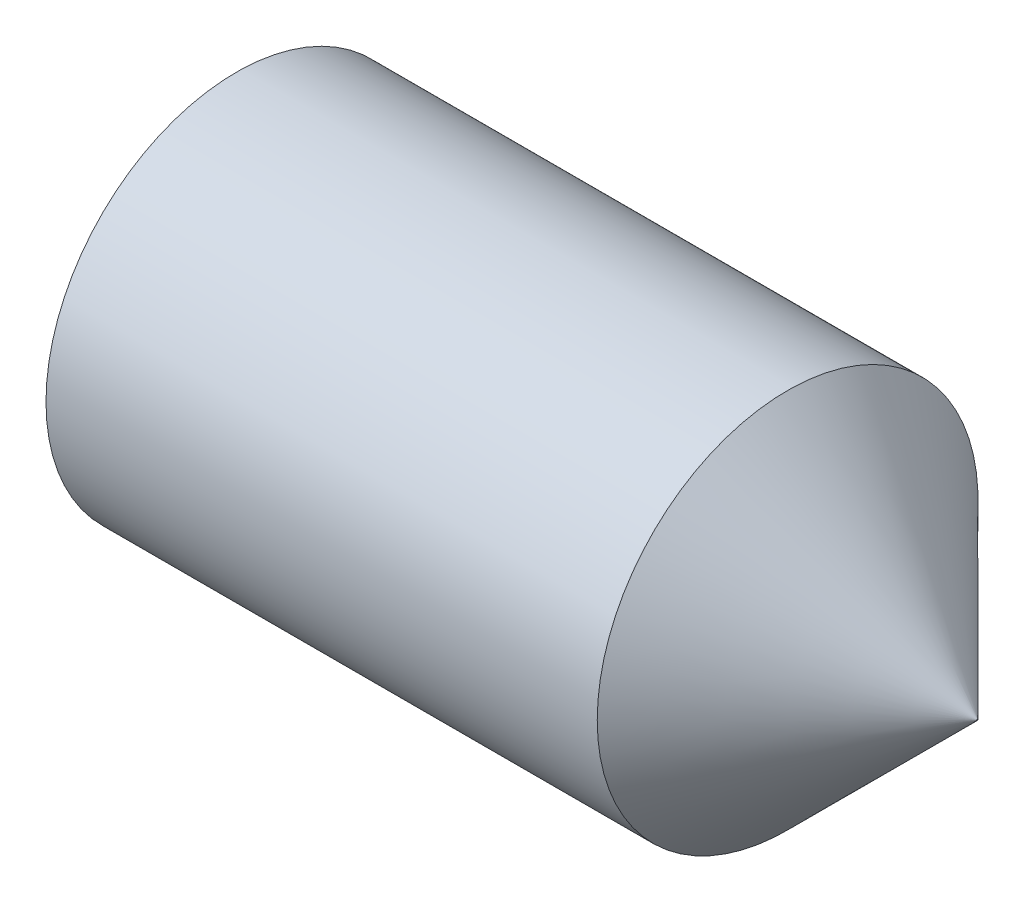
SolidWorks part; units mm, degrees
ref_plane "Plane1" through (0, 0, 0) normal (0, 0, 1) x (1, 0, 0)
ref_plane "Plane2" through (0, 0, 0) normal (0, 1, 0) x (1, 0, 0)
ref_plane "Plane3" through (0, 0, 0) normal (1, 0, 0) x (0, 0, -1)
sketch "BodySke" plane through (0, 0, 0) normal (0, 0, 1) x (1, 0, 0)
  line L0 (0, 0) -> (0, 1.2195)
  line L1 (0, 1.2195) -> (0.1619, 1.5)
  line L2 (0.1619, 1.5) -> (4.505, 1.5)
  line L3 (6, 0) -> (6, 0.005)
  line L4 (6, 0) -> (0, 0)
  line L5 (-12.7, 0) -> (88.9, 0) construction
  line L6 (6, 0.005) -> (4.505, 1.5)
  line L7 (0.5, 15.875) -> (0.5, -3.175) construction
  line L8 (0, -1.2195) -> (0.1619, -1.5) construction
  line L9 (6, -0.005) -> (4.505, -1.5) construction
  dimension "Cone_ang" = 90
  dimension "Length" = 6
  dimension "Diameter" = 3
  dimension "Drive_ch_ang" = 60
  dimension "Minor_dia" = 2.439
  dimension "Advance" = 0.5
  dimension "Tip_dia" = 0.01
revolve "BaseBody" add sketch "BodySke" angle 360 about L5
cosmetic thread "ThreadCosmetic" [suppressed] parameters "Thread_minor"=2.439
sketch "Sketch2" plane through (0, 0, 0) normal (-1, 0, 0) x (0, 0, 1)
  line L0 (0.433, 0.75) -> (-0.433, 0.75)
  line L1 (-0.433, 0.75) -> (-0.866, 0)
  line L2 (0.433, 0.75) -> (0.866, 0)
  line L3 (0.433, -0.75) -> (0.866, 0)
  line L4 (0.433, -0.75) -> (-0.433, -0.75)
  line L5 (-0.433, -0.75) -> (-0.866, 0)
  dimension "Hex_size" = 1.5
  dimension "D2" = 0.75
  dimension "D3" = 0.75
extrude "Hex" cut sketch "Sketch2" against normal blind 2.1
sketch "Sketch4" [suppressed] plane through (0, 4.7709, -0.5249) normal (-1, 0, 0) x (0, 0, 1)
  line L0 (0.5249, -4.7709) -> (10.6976, -4.7709)
  line L1 (0.5249, -4.7709) -> (6.6732, -1.2211) construction
  line L2 (0.5249, -4.7709) -> (5.6112, 4.0389)
  line L3 (8.9666, -2.6687) -> (10.2861, -1.9069)
  line L4 (6.5663, 1.4888) -> (7.8858, 2.2506)
  arc A0 (8.9666, -2.6687) -> (6.5663, 1.4888) centre (0.5249, -4.7709) ccw
  arc A1 (10.6976, -4.7709) -> (10.2861, -1.9069) centre (0.5249, -4.7709) ccw
  arc A2 (5.6112, 4.0389) -> (7.8858, 2.2506) centre (0.5249, -4.7709) cw
  circle A3 centre (0.5249, -4.7709) radius 8.6995 construction
  circle A4 centre (0.5249, -4.7709) radius 10.1727 construction
  dimension "D1" = 30
  dimension "Spline_n_dim" = 1.295
  dimension "Spline_m_dim" = 1.575
  dimension "Spline_a_dim" = 60
  dimension "D3" = 0.178
  dimension "Spline_p_dim" = 0.356
extrude "Spline6" [suppressed] cut sketch "Sketch4" against normal blind 1.2
pattern_circular "CirPattern1" [suppressed] count 6 every 60 about axis through (-12.7, 0, 0) along (1, 0, 0)
sketch "Sketch5" [suppressed] plane through (0, 1.4735, 6.925) normal (-1, 0, 0) x (0, 0, 1)
  line L0 (-6.925, -1.4735) -> (3.2477, -1.4735)
  line L1 (-6.925, -1.4735) -> (-1.9049, 3.5466) construction
  line L2 (-6.925, -1.4735) -> (-6.925, 8.6992)
  line L3 (0.9237, 2.9807) -> (1.7623, 3.8193)
  line L4 (-2.4708, 6.3752) -> (-1.6322, 7.2139)
  line L5 (-2.4708, 6.3752) -> (0.9237, 2.9807)
  arc A1 (3.2477, -1.4735) -> (1.7623, 3.8193) centre (-6.925, -1.4735) ccw
  arc A2 (-6.925, 8.6992) -> (-1.6322, 7.2139) centre (-6.925, -1.4735) cw
  circle A3 centre (-6.925, -1.4735) radius 8.6995 construction
  circle A4 centre (-6.925, -1.4735) radius 10.1727 construction
  dimension "D1" = 45
  dimension "Spline_n_dim" = 1.295
  dimension "Spline_m_dim" = 1.575
  dimension "Spline_a_dim" = 90
  dimension "D3" = 0.178
  dimension "Spline_p_dim" = 0.356
extrude "Spline4" [suppressed] cut sketch "Sketch5" against normal blind 1.2
pattern_circular "CirPattern2" [suppressed] count 4 every 90 about axis through (-12.7, 0, 0) along (1, 0, 0)
sketch "ThdSchSke" [suppressed] plane through (0, 0, 0) normal (0, 0, 1) x (1, 0, 0)
  line L0 (0.9515, -10.352) -> (-0.2025, -12)
  line L1 (0.9515, -10.352) -> (2.1054, -12)
  line L2 (2.1054, -12) -> (2.1054, -15)
  line L3 (-3.175, 0) -> (5.1513, 0) construction
  line L4 (0.9515, 12) -> (0.9515, -12) construction
  line L5 (2.1054, -15) -> (-0.2025, -15)
  line L6 (-0.2025, -15) -> (-0.2025, -12)
  dimension "Thread_minor" = 2.439
  dimension "Diameter" = 3
  dimension "SideAngle" = 55
  dimension "VeeAngle" = 70
  dimension "Overcut" = 3.75
revolve "ThreadSchematic" [suppressed] cut sketch "ThdSchSke" angle 360 about L3
pattern_linear "ThdSchPat" [suppressed]
equation "\"D2@Sketch2\" = \"Hex_size@Sketch2\" / 2"
equation "\"D3@Sketch2\" = \"Hex_size@Sketch2\" / 2"
equation "\"Thread_minor@ThreadCosmetic\" = \"Minor_dia@BodySke\""
equation "\"D1@Sketch4\" = \"Spline_a_dim@Sketch4\" / 2"
equation "\"D3@Sketch4\" = \"Spline_p_dim@Sketch4\" / 2"
equation "\"D2@CirPattern1\" = \"Spline_a_dim@Sketch4\""
equation "\"Num_teeth@CirPattern1\" = 360 / \"D2@CirPattern1\""
equation "\"Spline_a_dim@Sketch5\" = 90"
equation "\"Spline_p_dim@Sketch5\" = \"Spline_p_dim@Sketch4\""
equation "\"Spline_m_dim@Sketch5\" = \"Spline_m_dim@Sketch4\""
equation "\"Spline_n_dim@Sketch5\" = \"Spline_n_dim@Sketch4\""
equation "\"D1@Sketch5\" = \"Spline_a_dim@Sketch5\" / 2"
equation "\"D3@Sketch5\" = \"Spline_p_dim@Sketch5\" / 2"
equation "\"Key_eng@Spline4\" = \"Key_eng@Spline6\""
equation "\"Thread_minor@ThdSchSke\" = \"Thread_minor@ThreadCosmetic\""
equation "\"Diameter@ThdSchSke\" = \"Diameter@BodySke\""
equation "\"Overcut@ThdSchSke\" = \"Diameter@BodySke\" * 1.25"
equation "\"Num_threads@ThdSchPat\" = int( (\"Length@BodySke\" - ( ( ( \"Diameter@BodySke\" - \"Minor_dia@BodySke\" ) * 0.5 ) / tan( \"Drive_ch_ang@BodySke\" * 0.017453292 ) ) - ( ( \"Diameter@BodySke\" * 0.5 ) / tan( \"Cone_ang@BodySke\" * 0.008726646 ) ) ) / \"Advance@BodySke\" + 0.999 )  + 1"
equation "\"Num_threads@ThdSchPat\" = int( (\"Length@BodySke\" - ( ( ( \"Diameter@BodySke\" - \"Minor_dia@BodySke\" ) * 0.5 ) / tan( \"Drive_ch_ang@BodySke\" * 0.017453292 ) ) - ( (( \"Diameter@BodySke\" - \"Tip_dia@BodySke\") * 0.5 ) / tan( \"Cone_ang@BodySke\" * 0.008726646 ) ) ) / \"Advance@BodySke\" + 0.999 )  + 1"
equation "\"Advance@ThdSchPat\" = (\"Length@BodySke\" - ( ( ( \"Diameter@BodySke\" - \"Minor_dia@BodySke\" ) * 0.5 ) / tan( \"Drive_ch_ang@BodySke\" * 0.017453292 ) ) - ( ( \"Diameter@BodySke\" * 0.5 ) / tan( \"Cone_ang@BodySke\" * 0.008726646 ) ) ) /  (\"Num_threads@ThdSchPat\" - 1) 'relax it"
equation "\"Advance@ThdSchPat\" = (\"Length@BodySke\" - ( ( ( \"Diameter@BodySke\" - \"Minor_dia@BodySke\" ) * 0.5 ) / tan( \"Drive_ch_ang@BodySke\" * 0.017453292 ) ) - ( ( (\"Diameter@BodySke\" - \"Tip_dia@BodySke\") * 0.5 ) / tan( \"Cone_ang@BodySke\" * 0.008726646 ) ) ) /  (\"Num_threads@ThdSchPat\" - 1) 'relax it"
equation "' \"Num_threads@ThdSchPat\" = \"Num_threads@ThdSchPat\" - sgn( \"Num_threads@ThdSchPat\" - 1) '---chamfered tips only---"
